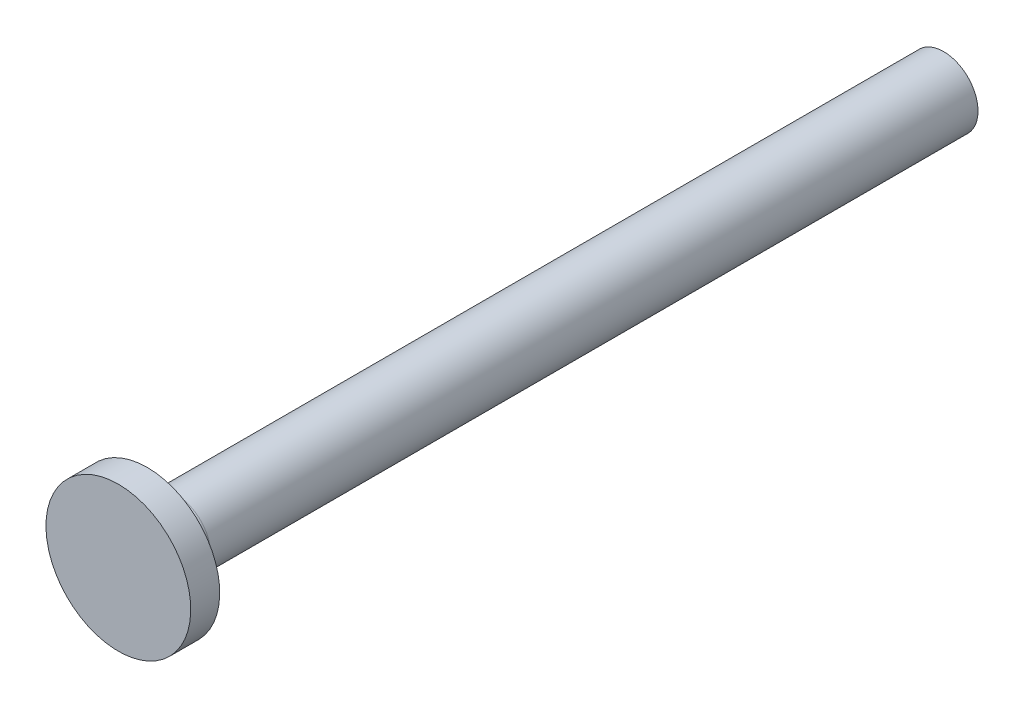
SolidWorks part; units mm, degrees
material "Alloy Steel"
ref_plane "Front Plane" through (0, 0, 0) normal (1, 0, 0) x (0, 1, 0)
ref_plane "Top Plane" through (0, 0, 0) normal (0, 0, 1) x (0, 1, 0)
ref_plane "Right Plane" through (0, 0, 0) normal (0, 1, 0) x (-1, 0, 0)
sketch "Sketch1" plane through (0, 0, 0) normal (1, 0, 0) x (0, 1, 0)
  line L0 (0, -55) -> (0, 2)
  line L1 (0, 2) -> (-5, 2)
  line L2 (-5, 2) -> (-5, 0)
  line L3 (-5, 0) -> (-2.375, 0)
  line L4 (-2.375, 0) -> (-2.375, -55)
  line L5 (-2.375, -55) -> (0, -55)
  point P0 (0, 0)
  dimension "D1" = 2.375
  dimension "D2" = 55
  dimension "D3" = 5
  dimension "D4" = 2
revolve "Revolve1" add sketch "Sketch1" angle 360 about L0
sketch "Sketch2" plane through (0, 0, 0) normal (1, 0, 0) x (0, 1, 0)
  line L0 (-13.1563, -2) -> (13.988, -2)
  line L1 (-2.375, -55) -> (2.375, -55) construction
  dimension "D1" = 53
split line "Split Line1"
